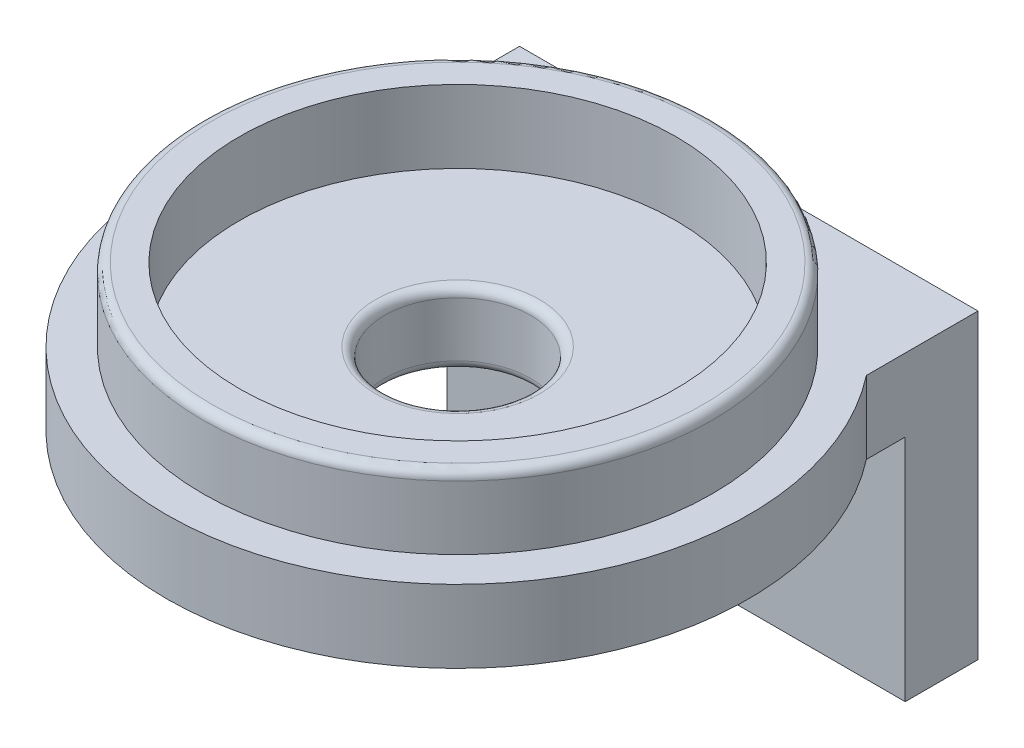
SolidWorks part; units mm, degrees
material "PLA Black"
ref_plane "Front Plane" through (0, 0, 0) normal (0, 0, 1) x (1, 0, 0)
ref_plane "Top Plane" through (0, 0, 0) normal (0, 1, 0) x (1, 0, 0)
ref_plane "Right Plane" through (0, 0, 0) normal (1, 0, 0) x (0, 0, -1)
sketch "Sketch1" plane through (0, 0, 0) normal (1, 0, 0) x (0, 0, -1)
  line L0 (0, -32.3252) -> (0, 32.3252) construction
  line L1 (22.225, 9.525) -> (22.225, 3.175)
  line L2 (22.225, 3.175) -> (25.4, 3.175)
  line L3 (25.4, 3.175) -> (25.4, -3.175)
  line L8 (19.05, 9.525) -> (22.225, 9.525)
  line L13 (19.05, 3.175) -> (19.05, 9.525)
  line L14 (19.05, 3.175) -> (6.35, 3.175)
  line L15 (6.35, 3.175) -> (6.35, -3.175)
  line L16 (6.35, -3.175) -> (25.4, -3.175)
  point P4 (0, 0)
  point P12 (25.4, 0)
  dimension "D1" = 3.175
  dimension "D2" = 6.35
  dimension "D3" = 6.35
  dimension "D4" = 50.8
  dimension "D5" = 12.7
revolve "Revolve1" add sketch "Sketch1" angle 360 about L0
fillet "Fillet1" radius 0.7937 3 edges at (0, 9.525, -22.225) (0, -3.175, -6.35) (0, 3.175, -6.35)
sketch "Sketch2" plane through (0, 0, 0) normal (1, 0, 0) x (0, 0, -1)
  line L0 (-25.4, -3.175) -> (25.4, -3.175) construction
  line L1 (25.4, 3.175) -> (12.7, 3.175)
  line L2 (25.4, 3.175) -> (25.4, -3.175)
  line L3 (19.05, -3.175) -> (12.7, -3.175)
  line L4 (12.7, 3.175) -> (12.7, -3.175)
  line L5 (25.4, 3.175) -> (12.7, -3.175) construction
  line L6 (25.4, -3.175) -> (12.7, 3.175) construction
  line L9 (25.4, -3.175) -> (25.4, -23.175)
  line L10 (25.4, -23.175) -> (19.05, -23.175)
  line L11 (19.05, -3.175) -> (19.05, -23.175)
  line L12 (25.4, -3.175) -> (19.05, -23.175) construction
  line L13 (25.4, -23.175) -> (19.05, -3.175) construction
  point P4 (19.05, 0)
  point P11 (22.225, -13.175)
  dimension "D1" = 12.7
  dimension "D2" = 20
  dimension "D3" = 6.35
extrude "Boss-Extrude1" add sketch "Sketch2" along normal mid plane 40
sketch "Sketch3" plane through (0, 0, -19.05) normal (0, 0, 1) x (1, 0, 0)
  arc A0 (-10, -15.275) -> (-10, -11.075) centre (-10, -13.175) ccw construction
  arc A1 (10, -15.275) -> (10, -11.075) centre (10, -13.175) ccw construction
  arc A2 (-10, -15.275) -> (-10, -11.075) centre (-10, -13.175) ccw
  arc A3 (10, -15.275) -> (10, -11.075) centre (10, -13.175) ccw
  circle A4 centre (-10, -13.175) radius 2.1
  circle A5 centre (10, -13.175) radius 2.1
extrude "Cut-Extrude1" cut sketch "Sketch3" against normal through all contours A2 A4 | A3 A5
